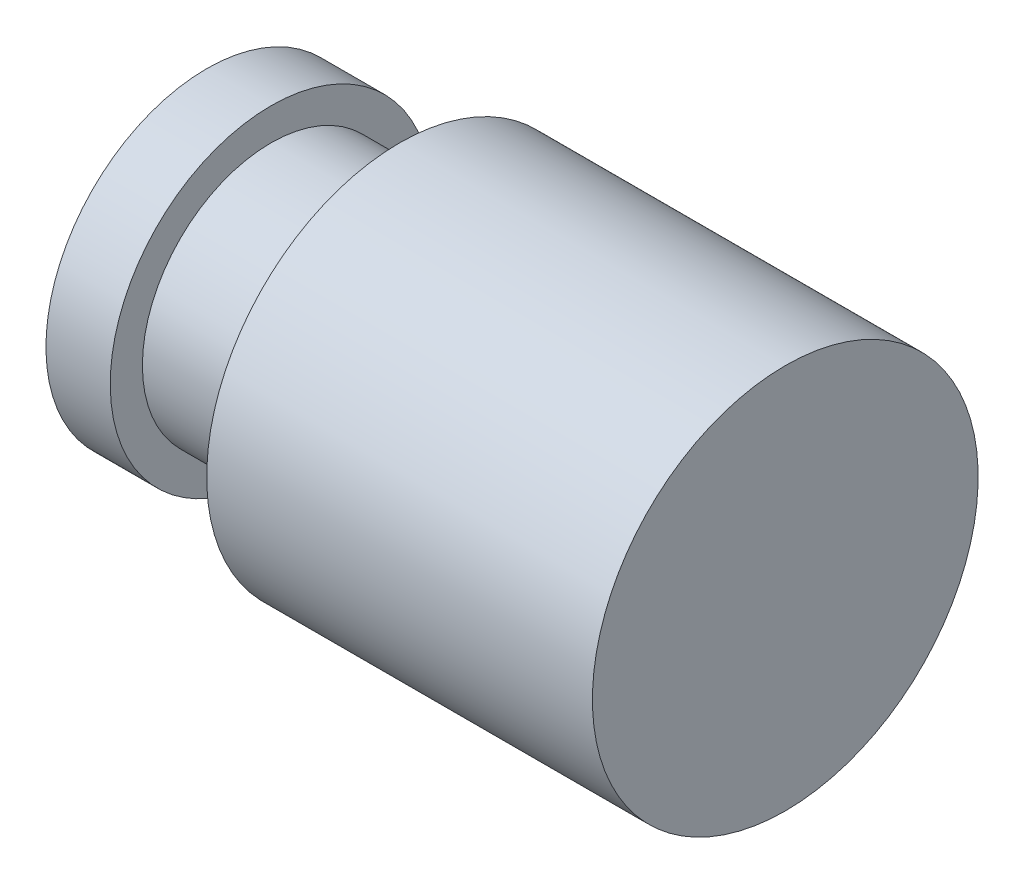
SolidWorks part; units mm, degrees
ref_plane "Face" through (0, 0, 0) normal (0, 0, 1) x (1, 0, 0)
ref_plane "Dessus" through (0, 0, 0) normal (0, 1, 0) x (1, 0, 0)
ref_plane "Droite" through (0, 0, 0) normal (1, 0, 0) x (0, 0, -1)
sketch "Esquisse1" plane through (0, 0, 0) normal (0, 0, 1) x (1, 0, 0)
  line L0 (0, 0) -> (0, 2.5)
  line L1 (0, 2.5) -> (1, 2.5)
  line L2 (1, 2.5) -> (1, 2)
  line L3 (3, 2) -> (3, 3)
  line L4 (3, 3) -> (9, 3)
  line L6 (9, 0) -> (0, 0)
  line L7 (1, 2) -> (3, 2)
  line L8 (9, 3) -> (9, 2)
  line L10 (9, 2) -> (9, 0)
  dimension "D1" = 2.5
  dimension "D2" = 1
  dimension "D3" = 2
  dimension "D4" = 2
  dimension "D5" = 3
  dimension "D6" = 6
revolve "Révolution1" add sketch "Esquisse1" angle 360 about L6
